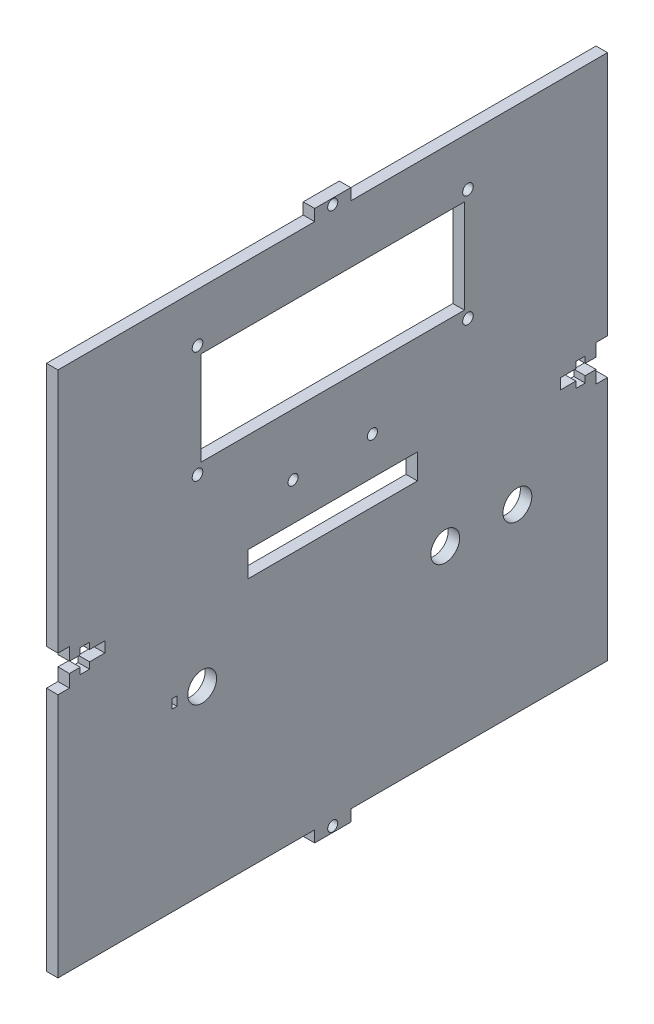
SolidWorks part; units mm, degrees
ref_plane "Front Plane" through (0, 0, 0) normal (0, 0, 1) x (1, 0, 0)
ref_plane "Top Plane" through (0, 0, 0) normal (0, 1, 0) x (1, 0, 0)
ref_plane "Right Plane" through (0, 0, 0) normal (1, 0, 0) x (0, 0, -1)
sketch "Sketch1" plane through (0, 0, 0) normal (1, 0, 0) x (0, 0, -1)
  line L1 (76.2, 73.02) -> (-76.2, 73.02)
  line L2 (76.2, 73.02) -> (76.2, -73.02)
  line L3 (76.2, -73.02) -> (-76.2, -73.02)
  line L4 (-76.2, 73.02) -> (-76.2, -73.02)
  line L5 (76.2, 73.02) -> (-76.2, -73.02) construction
  line L6 (76.2, -73.02) -> (-76.2, 73.02) construction
  point P0 (0, 0)
  dimension "D1" = 146.04
  dimension "D2" = 152.4
extrude "Boss-Extrude1" add sketch "Sketch1" along normal blind 3.18
sketch "Sketch3" plane through (0, 0, 0) normal (-1, 0, 0) x (0, 0, 1)
  line L1 (0, 0) -> (-76.2, 0) construction
  line L2 (-76.2, -73.02) -> (-76.2, 73.02) construction
  line L3 (0, -73.02) -> (0, 73.02) construction
  line L9 (0, 0) -> (76.2, 0) construction
  line L10 (76.2, -73.02) -> (-76.2, -73.02) construction
  line L12 (76.2, 73.02) -> (76.2, -73.02) construction
  line L13 (-76.2, 73.02) -> (76.2, 73.02) construction
  line L14 (5, -73.02) -> (-5, -73.02)
  line L15 (5, -76.2) -> (-5, -76.2)
  line L16 (5, -76.2) -> (5, -73.02)
  line L18 (-5, -76.2) -> (-5, -73.02)
  line L22 (0, -76.2) -> (0, -70.042) construction
  line L23 (5, -74.61) -> (-5, -74.61) construction
  line L27 (5, 73.02) -> (5, 76.2)
  line L28 (5, 76.2) -> (-5, 76.2)
  line L29 (-5, 73.02) -> (-5, 76.2)
  line L30 (5, 74.61) -> (-5, 74.61) construction
  line L31 (0, 73.02) -> (0, 76.2) construction
  line L32 (5, 73.02) -> (-5, 73.02)
  line L33 (0, 57.9987) -> (0, 73.02)
  circle A0 centre (0, -74.61) radius 1.4
  circle A1 centre (0, 74.61) radius 1.4
  point P31 (0, 65.5094)
  line M14 (76.2, 73.02) -> (-76.2, 73.02)
  line M16 (-76.2, -73.02) -> (76.2, -73.02)
  dimension "D5" = 2.8
  dimension "D6" = 2.8
  dimension "D2" = 10
  dimension "D3" = 3.18
  dimension "D4" = 10
  dimension "D1" = 3.18
extrude "Boss-Extrude5" add sketch "Sketch3" against normal blind 3.18 contours L29 L32 L27 L28 A1 M14 | L18 L15 L16 A0 M16
sketch "Sketch4" plane through (0, 0, 0) normal (1, 0, 0) x (0, 0, -1)
  line L2 (0, 0) -> (-76.2, 0) construction
  line L3 (-76.2, 73.02) -> (-76.2, -73.02) construction
  line L4 (-76.2, -5) -> (-76.2, 5)
  line L5 (-76.2, -5) -> (-73.02, -5)
  line L7 (-76.2, 5) -> (-73.02, 5)
  line L8 (-73.02, -5) -> (-73.02, -1.47)
  line L9 (-73.02, 1.47) -> (-73.02, 5)
  line L10 (-73.02, -1.47) -> (-70.02, -1.47)
  line L12 (-73.02, 1.47) -> (-70.02, 1.47)
  line L13 (-63.2, -1.47) -> (-63.2, 1.47)
  line L14 (-67.42, -1.47) -> (-63.2, -1.47)
  line L15 (-70.02, -3.25) -> (-67.42, -3.25)
  line L16 (-70.02, -3.25) -> (-70.02, -1.47)
  line L17 (-70.02, 3.25) -> (-67.42, 3.25)
  line L18 (-67.42, -3.25) -> (-67.42, -1.47)
  line L19 (-67.42, 1.47) -> (-63.2, 1.47)
  line L20 (-70.02, 1.47) -> (-70.02, 3.25)
  line L21 (-67.42, 1.47) -> (-67.42, 3.25)
  dimension "D1" = 3.18
  dimension "D2" = 10
  dimension "D3" = 2.94
  dimension "D4" = 6.5
  dimension "D5" = 2.6
  dimension "D6" = 13
  dimension "D7" = 3
extrude "Cut-Extrude2" cut sketch "Sketch4" along normal through all contours L18 L14 L13 L19 L21 L17 L20 L12 L9 L7 L4 L5 L8 L10 L16 L15
sketch "Sketch5" plane through (0, 0, 0) normal (-1, 0, 0) x (0, 0, 1)
  line L0 (0, 0) -> (-76.2, 0) construction
  line L1 (-76.2, -73.02) -> (-76.2, 73.02) construction
  line L2 (-70.02, -1.47) -> (-73.02, -1.47)
  line L3 (-76.2, -5) -> (-73.02, -5)
  line L4 (-76.2, -5) -> (-76.2, 5)
  line L5 (-76.2, 5) -> (-73.02, 5)
  line L6 (-73.02, -5) -> (-73.02, -1.47)
  line L7 (-63.2, -1.47) -> (-67.42, -1.47)
  line L8 (-63.2, -1.47) -> (-63.2, 1.47)
  line L9 (-63.2, 1.47) -> (-67.42, 1.47)
  line L13 (-67.42, 3.25) -> (-70.02, 3.25)
  line L14 (-67.42, 3.25) -> (-67.42, 1.47)
  line L15 (-67.42, -3.25) -> (-70.02, -3.25)
  line L16 (-70.02, 3.25) -> (-70.02, 1.47)
  line L17 (-70.02, -1.47) -> (-70.02, -3.25)
  line L20 (-67.42, -1.47) -> (-67.42, -3.25)
  line L22 (-70.02, 1.47) -> (-73.02, 1.47)
  line L23 (-73.02, 1.47) -> (-73.02, 5)
  point P9 (-39.8999, 0)
  dimension "D1" = 10
  dimension "D2" = 3.18
  dimension "D3" = 3
  dimension "D4" = 2.6
  dimension "D5" = 2.6
  dimension "D6" = 2.94
  dimension "D7" = 13
  dimension "D8" = 6.5
  dimension "D9" = 6.5
  dimension "D10" = 4.22
extrude "Cut-Extrude3" cut sketch "Sketch5" against normal through all
sketch "Sketch6" plane through (0, 0, 0) normal (-1, 0, 0) x (0, 0, 1)
  line L0 (0, 76.2) -> (0, 0) construction
  line L1 (5, 76.2) -> (-5, 76.2) construction
  line L2 (-76.2, 73.02) -> (-5, 73.02) construction
  line L3 (-36.5, 57.02) -> (36.5, 57.02)
  line L4 (-36.5, 57.02) -> (-36.5, 31.02)
  line L5 (-36.5, 31.02) -> (36.5, 31.02)
  line L6 (36.5, 57.02) -> (36.5, 31.02)
  point P5 (0, 38.1)
  dimension "D1" = 26
  dimension "D2" = 73
  dimension "D3" = 16
extrude "Cut-Extrude4" cut sketch "Sketch6" against normal blind 10
sketch "Sketch7" plane through (0, 0, 0) normal (-1, 0, 0) x (0, 0, 1)
  line L0 (-36.5, 57.02) -> (-36.5, 31.02) construction
  line L1 (36.5, 31.02) -> (36.5, 57.02) construction
  line L2 (0, 57.02) -> (0, 31.02) construction
  line L3 (36.5, 57.02) -> (-36.5, 57.02) construction
  line L4 (-36.5, 31.02) -> (36.5, 31.02) construction
  line L5 (-36.5, 44.02) -> (36.5, 44.02) construction
  circle A0 centre (-37.5, 59.52) radius 1.47
  circle A1 centre (-37.5, 28.52) radius 1.47
  circle A2 centre (37.5, 59.52) radius 1.47
  circle A3 centre (37.5, 28.52) radius 1.47
  dimension "D1" = 75
  dimension "D2" = 31
  dimension "D6" = 2.94
extrude "Cut-Extrude5" cut sketch "Sketch7" against normal through all
sketch "Sketch8" plane through (0, 0, 0) normal (-1, 0, 0) x (0, 0, 1)
  line L0 (-76.2, -73.02) -> (-76.2, -5) construction
  line L1 (-5, -73.02) -> (-76.2, -73.02) construction
  line L2 (76.2, -5) -> (76.2, -73.02) construction
  line L3 (76.2, -73.02) -> (5, -73.02) construction
  circle A0 centre (-51.2, -23.02) radius 4
  circle A1 centre (-31.2, -23.02) radius 4
  circle A2 centre (36.2, -23.02) radius 4
  dimension "D1" = 8
  dimension "D2" = 8
  dimension "D3" = 25
  dimension "D4" = 50
  dimension "D5" = 45
  dimension "D6" = 50
  dimension "D7" = 8
  dimension "D8" = 40
  dimension "D9" = 50
extrude "Cut-Extrude6" cut sketch "Sketch8" against normal through all
sketch "Sketch9" plane through (0, 0, 0) normal (-1, 0, 0) x (0, 0, 1)
  line L1 (-23.5, 3.5) -> (23.5, 3.5)
  line L2 (-23.5, 3.5) -> (-23.5, -3.5)
  line L3 (-23.5, -3.5) -> (23.5, -3.5)
  line L4 (23.5, 3.5) -> (23.5, -3.5)
  line L5 (-23.5, 3.5) -> (23.5, -3.5) construction
  line L6 (-23.5, -3.5) -> (23.5, 3.5) construction
  point P0 (0, 0)
  dimension "D1" = 7
  dimension "D2" = 47
extrude "Cut-Extrude7" cut sketch "Sketch9" against normal through all and the other way through all
sketch "Sketch10" plane through (0, 0, 0) normal (-1, 0, 0) x (0, 0, 1)
  line L0 (32.2, -23.02) -> (40.2, -23.02) construction
  line L1 (44.51, -21.77) -> (43.2, -21.77)
  line L2 (44.51, -21.77) -> (44.51, -24.27)
  line L3 (44.51, -24.27) -> (43.2, -24.27)
  line L4 (43.2, -21.77) -> (43.2, -24.27)
  line L5 (44.51, -21.77) -> (43.2, -24.27) construction
  line L6 (44.51, -24.27) -> (43.2, -21.77) construction
  line L7 (40.2, -23.02) -> (47.51, -23.02) construction
  circle A0 centre (36.2, -23.02) radius 4 construction
  point P0 (43.855, -23.02)
  dimension "D1" = 1.31
  dimension "D2" = 2.5
  dimension "D3" = 7
extrude "Cut-Extrude8" cut sketch "Sketch10" against normal through all
sketch "Sketch11" plane through (0, 0, 0) normal (-1, 0, 0) x (0, 0, 1)
  line L0 (0, 76.01) -> (0, 3.5) construction
  line L1 (23.5, 3.5) -> (-23.5, 3.5) construction
  line L4 (-36.5, 31.02) -> (36.5, 31.02) construction
  circle A0 centre (0, 74.61) radius 1.4 construction
  circle A1 centre (-11, 14.02) radius 1.4
  circle A2 centre (11, 14.02) radius 1.4
  dimension "D1" = 2.8
  dimension "D2" = 22
  dimension "D3" = 17
extrude "Cut-Extrude9" cut sketch "Sketch11" against normal through all
equation "\"sheet\"= 3.18mm"
equation "\"tabW\"= 15mm"
equation "\"4-40Diam\" = 2.94mm"
equation "\"nutDiam\" = 6.5mm"
equation "\"nutThickness\"= 2.6mm"
